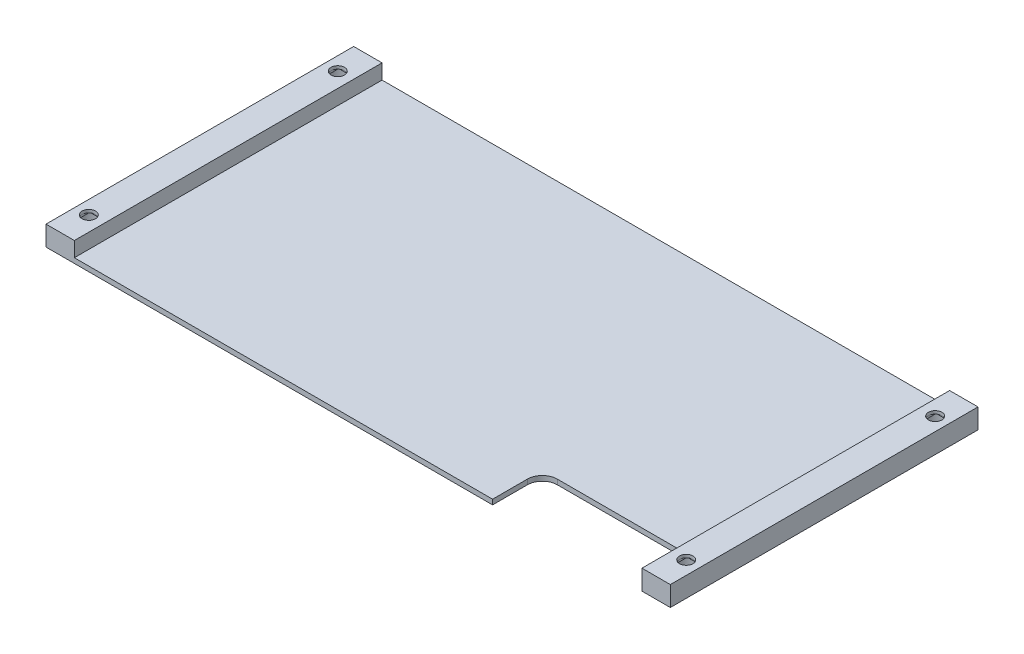
SolidWorks part; units mm, degrees
ref_plane "Front Plane" through (0, 0, 0) normal (0, 0, 1) x (1, 0, 0)
ref_plane "Top Plane" through (0, 0, 0) normal (0, 1, 0) x (1, 0, 0)
ref_plane "Right Plane" through (0, 0, 0) normal (1, 0, 0) x (0, 0, -1)
sketch "Sketch1" plane through (0, 0, 0) normal (0, 1, 0) x (1, 0, 0)
  line L1 (-63, -30.9) -> (63, -30.9)
  line L2 (-63, -30.9) -> (-63, 30.9)
  line L3 (-63, 30.9) -> (63, 30.9)
  line L4 (63, -30.9) -> (63, 30.9)
  line L5 (-63, -30.9) -> (63, 30.9) construction
  line L6 (-63, 30.9) -> (63, -30.9) construction
  point P0 (0, 0)
  dimension "D1" = 126
  dimension "D2" = 61.8
extrude "Boss-Extrude1" add sketch "Sketch1" along normal blind 1
sketch "Sketch2" plane through (0, 1, 0) normal (0, 1, 0) x (1, 0, 0)
  line L0 (-63, -30.9) -> (63, -30.9) construction
  line L1 (-63, 30.9) -> (-57, 30.9)
  line L2 (-63, 30.9) -> (-63, -30.9)
  line L3 (-63, -30.9) -> (-57, -30.9)
  line L4 (-57, 30.9) -> (-57, -30.9)
  line L6 (63, 30.9) -> (57, 30.9)
  line L7 (63, 30.9) -> (63, -30.9)
  line L8 (63, -30.9) -> (57, -30.9)
  line L9 (57, 30.9) -> (57, -30.9)
  dimension "D1" = 6
extrude "Boss-Extrude2" add sketch "Sketch2" along normal blind 3
sketch "Sketch3" plane through (0, 4, 0) normal (0, 1, 0) x (1, 0, 0)
  line L0 (-63, 30.9) -> (-57, -30.9) construction
  line L1 (-60, -25) -> (-60, 25) construction
  line L2 (0, 0) -> (0, 30.9) construction
  line L3 (57, 30.9) -> (-57, 30.9) construction
  line L4 (60, -25) -> (60, 25) construction
  line L5 (63, 30.9) -> (57, -30.9) construction
  circle A0 centre (-60, 25) radius 1.35
  circle A1 centre (-60, -25) radius 1.35
  circle A2 centre (60, -25) radius 1.35
  circle A3 centre (60, 25) radius 1.35
  point P7 (-60, 0)
  point P20 (60, 0)
  dimension "D1" = 2.7
  dimension "D2" = 50
extrude "Cut-Extrude1" cut sketch "Sketch3" against normal through all
sketch "Sketch4" plane through (0, 0, 0) normal (0, -1, 0) x (1, 0, 0)
  circle A0 centre (60, -25) radius 2.5
  circle A1 centre (60, 25) radius 2.5
  circle A2 centre (-60, 25) radius 2.5
  circle A3 centre (-60, -25) radius 2.5
  dimension "D1" = 5
extrude "Cut-Extrude2" cut sketch "Sketch4" against normal blind 3
sketch "Sketch5" plane through (0, 0, 0) normal (0, -1, 0) x (1, 0, 0)
  line L0 (-63, 30.9) -> (63, 30.9) construction
  line L1 (57, 30.9) -> (27, 30.9)
  line L2 (57, 30.9) -> (57, 20.9)
  line L3 (57, 20.9) -> (27, 20.9)
  line L4 (27, 30.9) -> (27, 20.9)
  line L6 (57, -30.9) -> (57, 30.9) construction
  dimension "D1" = 30
  dimension "D2" = 10
extrude "Cut-Extrude3" cut sketch "Sketch5" against normal through all
fillet "Fillet1" radius 3 2 edges at (27, 0.5, 20.9) (57, 0.5, 20.9)
sketch "Sketch6" plane through (0, 3, 0) normal (0, -1, 0) x (1, 0, 0)
  line L2 (-61.35, 22.8958) -> (-61.35, 27.1042)
  line L4 (-58.65, 22.8958) -> (-58.65, 27.1042)
  line L5 (-61.35, 22.8958) -> (-58.65, 27.1042) construction
  line L6 (-61.35, 27.1042) -> (-58.65, 22.8958) construction
  line L8 (-61.35, -27.1042) -> (-61.35, -22.8958)
  line L10 (-58.65, -27.1042) -> (-58.65, -22.8958)
  line L11 (-61.35, -27.1042) -> (-58.65, -22.8958) construction
  line L12 (-61.35, -22.8958) -> (-58.65, -27.1042) construction
  circle A0 centre (-60, 25) radius 2.5 construction
  arc A1 (-58.65, 27.1042) -> (-61.35, 27.1042) centre (-60, 25) ccw
  circle A2 centre (-60, 25) radius 1.35 construction
  arc A3 (-61.35, 22.8958) -> (-58.65, 22.8958) centre (-60, 25) ccw
  circle A4 centre (-60, -25) radius 2.5 construction
  arc A5 (-58.65, -22.8958) -> (-61.35, -22.8958) centre (-60, -25) ccw
  circle A6 centre (-60, -25) radius 1.35 construction
  arc A7 (-61.35, -27.1042) -> (-58.65, -27.1042) centre (-60, -25) ccw
  point P0 (-60, 25)
  point P8 (-60, -25)
extrude "Cut-Extrude4" cut sketch "Sketch6" against normal blind 0.2
sketch "Sketch7" plane through (0, 3.2, 0) normal (0, -1, 0) x (1, 0, 0)
  line L0 (-58.65, -25) -> (-58.65, -22.8958) construction
  line L1 (-61.35, -26.35) -> (-58.65, -26.35)
  line L2 (-61.35, -26.35) -> (-61.35, -23.65)
  line L3 (-61.35, -23.65) -> (-58.65, -23.65)
  line L4 (-58.65, -26.35) -> (-58.65, -23.65)
  line L5 (-61.35, -26.35) -> (-58.65, -23.65) construction
  line L6 (-61.35, -23.65) -> (-58.65, -26.35) construction
  line L7 (-58.65, 22.8958) -> (-58.65, 27.1042) construction
  line L8 (-61.35, 23.65) -> (-58.65, 23.65)
  line L9 (-61.35, 23.65) -> (-61.35, 26.35)
  line L10 (-61.35, 26.35) -> (-58.65, 26.35)
  line L11 (-58.65, 23.65) -> (-58.65, 26.35)
  line L12 (-61.35, 23.65) -> (-58.65, 26.35) construction
  line L13 (-61.35, 26.35) -> (-58.65, 23.65) construction
  arc A0 (-58.65, -25) -> (-61.35, -25) centre (-60, -25) ccw construction
  arc A1 (-58.65, 25) -> (-61.35, 25) centre (-60, 25) ccw construction
  point P0 (-60, -25)
  point P11 (-60, 25)
extrude "Cut-Extrude5" cut sketch "Sketch7" against normal blind 0.2
mirror "Mirror1" about plane through (0, 0, 0) normal (1, 0, 0) of "Cut-Extrude5", "Cut-Extrude4"
sketch "Sketch8" plane through (0, 4, 0) normal (0, 1, 0) x (1, 0, 0)
  line L0 (-63, -30.9) -> (-57, -30.9) construction
  line L1 (-63, 30.9) -> (-62.7, 30.9)
  line L2 (-63, 30.9) -> (-63, -30.9)
  line L3 (-63, -30.9) -> (-62.7, -30.9)
  line L4 (-62.7, 30.9) -> (-62.7, -30.9)
  line L5 (57, -30.9) -> (63, -30.9) construction
  line L6 (63, 30.9) -> (62.7, 30.9)
  line L7 (63, 30.9) -> (63, -30.9)
  line L8 (63, -30.9) -> (62.7, -30.9)
  line L9 (62.7, 30.9) -> (62.7, -30.9)
  dimension "D1" = 0.3
extrude "Cut-Extrude6" cut sketch "Sketch8" against normal through all
